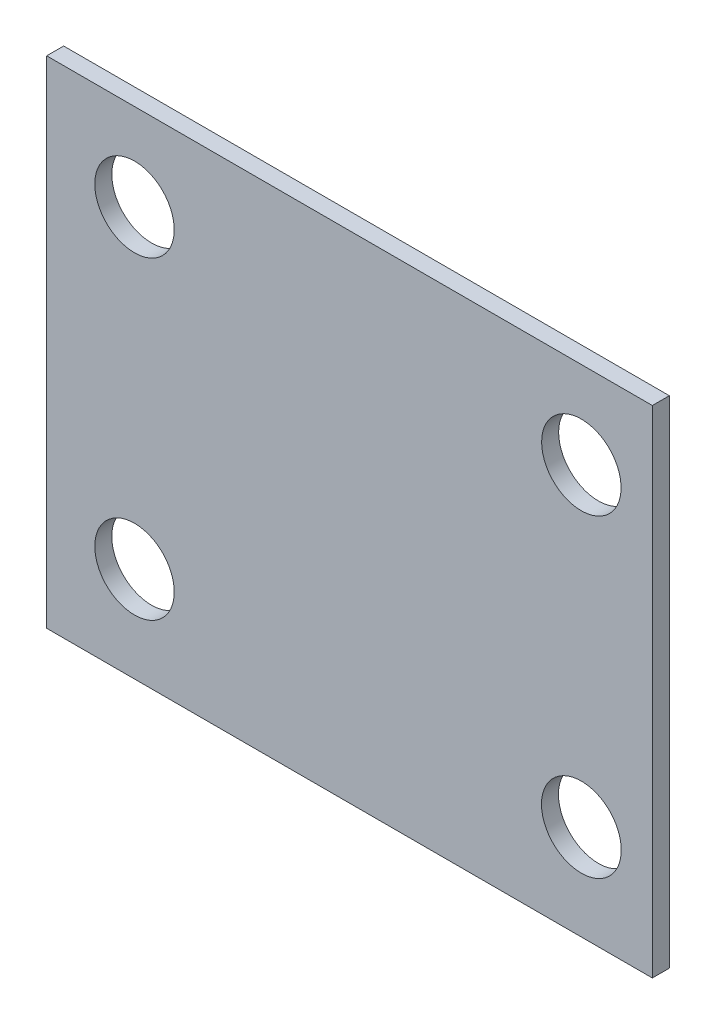
SolidWorks part; units mm, degrees
ref_plane "Front Plane" through (0, 0, 0) normal (0, 0, 1) x (1, 0, 0)
ref_plane "Top Plane" through (0, 0, 0) normal (0, 1, 0) x (1, 0, 0)
ref_plane "Right Plane" through (0, 0, 0) normal (1, 0, 0) x (0, 0, -1)
sketch "Sketch2" plane through (0, 0, 0) normal (0, 0, 1) x (1, 0, 0)
  line L1 (0, 0) -> (60.25, 0)
  line L2 (0, 0) -> (0, 49.32)
  line L3 (0, 49.32) -> (60.25, 49.32)
  line L4 (60.25, 0) -> (60.25, 49.32)
  dimension "D1" = 60.25
  dimension "D2" = 49.32
extrude "Boss-Extrude1" add sketch "Sketch2" along normal blind 1.69
sketch "Sketch3" plane through (0, 0, 0) normal (0, 0, -1) x (-1, 0, 0)
  line L0 (-5.7221, 43.2236) -> (-11.7557, 38.1173) construction
  circle A0 centre (-8.7389, 40.6704) radius 3.9521
  circle A1 centre (-53.1889, 40.6704) radius 3.9522
  circle A2 centre (-53.1889, 9.4665) radius 3.9687
  circle A3 centre (-8.7389, 9.4665) radius 3.9522
extrude "Cut-Extrude1" cut sketch "Sketch3" against normal through all
